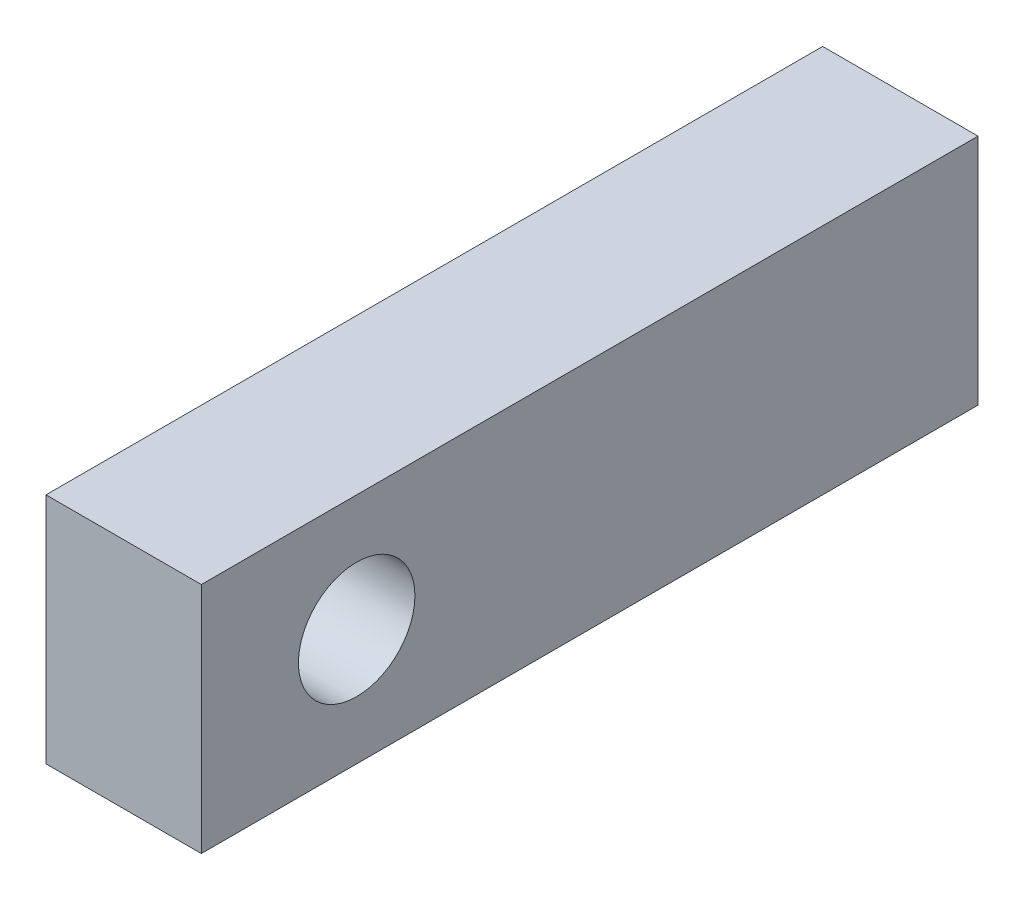
SolidWorks part; units mm, degrees
material "Pine"
ref_plane "Front Plane" through (0, 0, 0) normal (0, 0, 1) x (1, 0, 0)
ref_plane "Top Plane" through (0, 0, 0) normal (0, 1, 0) x (1, 0, 0)
ref_plane "Right Plane" through (0, 0, 0) normal (1, 0, 0) x (0, 0, -1)
sketch "Sketch1" plane through (0, 0, 0) normal (0, 0, 1) x (1, 0, 0)
  line L1 (0, 0) -> (25.4, 0)
  line L2 (0, 0) -> (0, 38.1)
  line L3 (0, 38.1) -> (25.4, 38.1)
  line L4 (25.4, 0) -> (25.4, 38.1)
  dimension "D1" = 38.1
  dimension "D2" = 25.4
extrude "Boss-Extrude1" add sketch "Sketch1" along normal blind 127
sketch "Sketch2" plane through (25.4, 0, 0) normal (1, 0, 0) x (0, 0, -1)
  line L0 (-127, 0) -> (-127, 38.1) construction
  line L1 (-127, 38.1) -> (0, 38.1) construction
  circle A0 centre (-101.6, 19.05) radius 9.525
  dimension "D1" = 19.05
  dimension "D2" = 25.4
  dimension "D3" = 19.05
extrude "Cut-Extrude1" cut sketch "Sketch2" against normal through all
